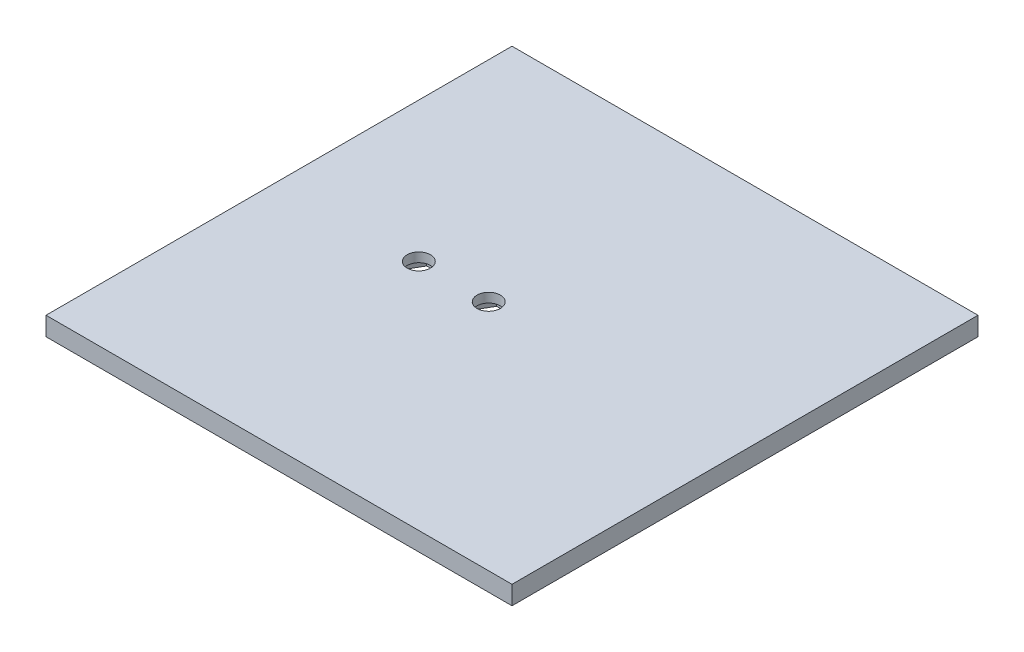
SolidWorks part; units mm, degrees
ref_plane "Front Plane" through (0, 0, 0) normal (0, 0, 1) x (1, 0, 0)
ref_plane "Top Plane" through (0, 0, 0) normal (0, 1, 0) x (1, 0, 0)
ref_plane "Right Plane" through (0, 0, 0) normal (1, 0, 0) x (0, 0, -1)
sketch "Sketch1" plane through (0, 0, 0) normal (0, 1, 0) x (1, 0, 0)
  line L1 (-34.8765, 23.534) -> (65.1235, 23.534)
  line L2 (-34.8765, 23.534) -> (-34.8765, -76.466)
  line L3 (-34.8765, -76.466) -> (65.1235, -76.466)
  line L4 (65.1235, 23.534) -> (65.1235, -76.466)
  point P22 (2.0874, -26.3153)
  dimension "D1" = 100
  dimension "D2" = 100
extrude "Boss-Extrude1" add sketch "Sketch1" along normal blind 4
sketch "Sketch3" plane through (0, 4, 0) normal (0, 1, 0) x (1, 0, 0)
  line L0 (-34.8765, -76.466) -> (65.1235, -76.466) construction
  line L1 (-34.8765, 23.534) -> (-34.8765, -76.466) construction
  circle A0 centre (-4.8765, -26.466) radius 2.5
  circle A1 centre (10.1235, -26.466) radius 2.5
  dimension "D5" = 5
  dimension "D6" = 5
  dimension "D1" = 50
  dimension "D2" = 50
  dimension "D3" = 30
  dimension "D4" = 15
extrude "Cut-Extrude1" cut sketch "Sketch3" against normal blind 2 contours A1 | A0
sketch "Sketch5" plane through (0, 0, 0) normal (0, -1, 0) x (1, 0, 0)
  line L0 (-34.8765, -23.534) -> (-34.8765, 76.466) construction
  line L1 (-0.2577, 26.466) -> (-2.5671, 30.466)
  line L2 (-2.5671, 30.466) -> (-7.1859, 30.466)
  line L3 (-7.1859, 30.466) -> (-9.4953, 26.466)
  line L4 (-9.4953, 26.466) -> (-7.1859, 22.466)
  line L5 (-7.1859, 22.466) -> (-2.5671, 22.466)
  line L6 (-2.5671, 22.466) -> (-0.2577, 26.466)
  line L7 (14.7423, 26.466) -> (12.4329, 30.466)
  line L8 (12.4329, 30.466) -> (7.8141, 30.466)
  line L9 (7.8141, 30.466) -> (5.5047, 26.466)
  line L10 (5.5047, 26.466) -> (7.8141, 22.466)
  line L11 (7.8141, 22.466) -> (12.4329, 22.466)
  line L12 (12.4329, 22.466) -> (14.7423, 26.466)
  line L13 (65.1235, -23.534) -> (-34.8765, -23.534) construction
  circle A0 centre (-4.8765, 26.466) radius 4 construction
  circle A1 centre (10.1235, 26.466) radius 4 construction
  point P18 (0, 0)
  point P19 (0, 0)
  dimension "D5" = 8
  dimension "D6" = 8
  dimension "D1" = 30
  dimension "D2" = 15
  dimension "D3" = 50
  dimension "D4" = 50
extrude "Cut-Extrude2" cut sketch "Sketch5" against normal blind 2
